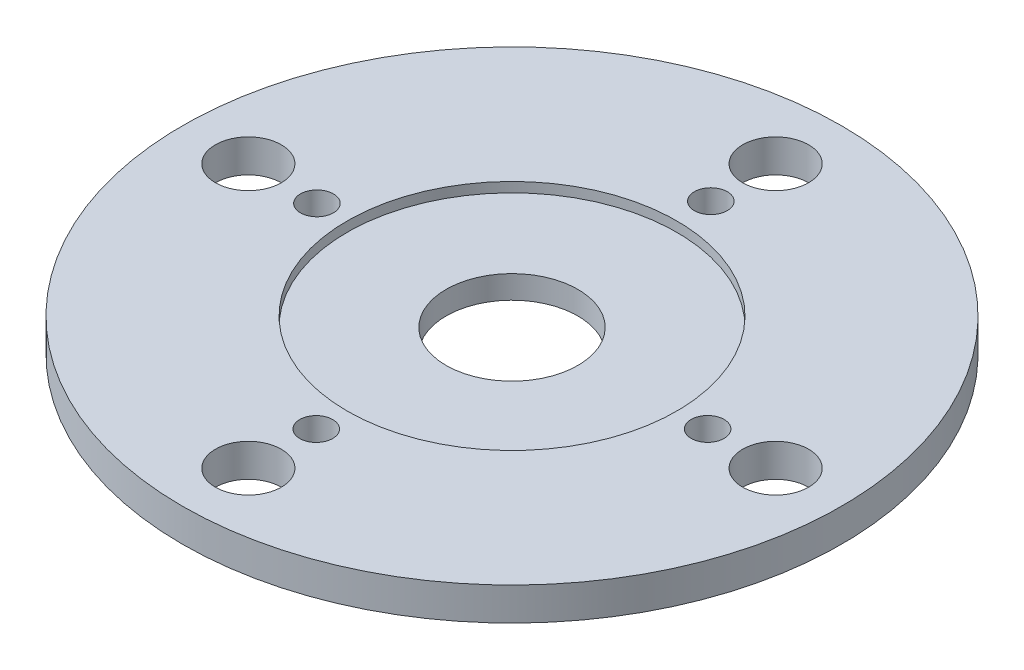
SolidWorks part; units mm, degrees
ref_plane "Front Plane" through (0, 0, 0) normal (0, 0, 1) x (1, 0, 0)
ref_plane "Top Plane" through (0, 0, 0) normal (0, 1, 0) x (1, 0, 0)
ref_plane "Right Plane" through (0, 0, 0) normal (1, 0, 0) x (0, 0, -1)
sketch "Sketch1" plane through (0, 0, 0) normal (0, 1, 0) x (1, 0, 0)
  line L6 (-10, 0) -> (0, 0) construction
  circle A0 centre (0, 0) radius 10
  circle A1 centre (0, 0) radius 2
  circle A2 centre (-8, 0) radius 1
  circle A3 centre (-5.9192, 0) radius 0.5
  circle A4 centre (0, -5.9414) radius 0.5
  circle A5 centre (0, -8) radius 1
  circle A6 centre (5.9368, 0) radius 0.5
  circle A7 centre (8, 0) radius 1
  circle A8 centre (0, 6.0334) radius 0.5
  circle A9 centre (0, 8) radius 1
  dimension "D1" = 20
  dimension "D2" = 4
  dimension "D3" = 2
  dimension "D4" = 1
  dimension "D5" = 8
  dimension "D6" = 8
  dimension "D7" = 8
  dimension "D8" = 8
extrude "Boss-Extrude1" add sketch "Sketch1" along normal blind 1
sketch "Sketch2" plane through (0, 1, 0) normal (0, 1, 0) x (1, 0, 0)
  circle A0 centre (0, 0) radius 5
  dimension "D1" = 10
extrude "Cut-Extrude1" cut sketch "Sketch2" against normal blind 0.3
